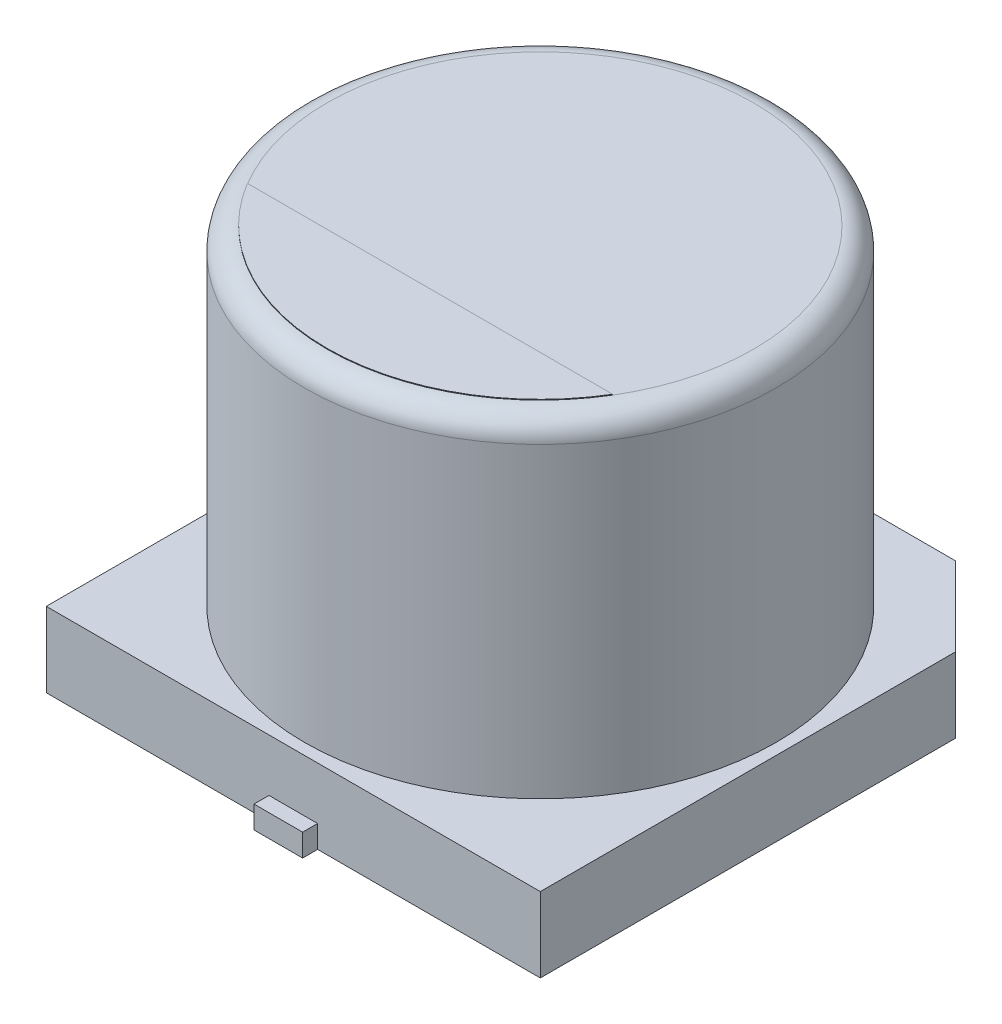
SolidWorks part; units mm, degrees
ref_plane "Front Plane" through (0, 0, 0) normal (0, 0, 1) x (1, 0, 0)
ref_plane "Top Plane" through (0, 0, 0) normal (0, 1, 0) x (1, 0, 0)
ref_plane "Right Plane" through (0, 0, 0) normal (1, 0, 0) x (0, 0, -1)
sketch "Sketch2" plane through (0, 0, 0) normal (0, 1, 0) x (1, 0, 0)
  line L0 (0, 0) -> (0, 2.085) construction
  line L1 (0, 0) -> (2.9643, 0) construction
  line L2 (3.3, -3.3) -> (-3.3, -3.3)
  line L3 (-3.3, -3.3) -> (-3.3, 2.25)
  line L4 (-3.3, 2.25) -> (-2.25, 3.3)
  line L5 (-2.25, 3.3) -> (2.25, 3.3)
  line L6 (2.25, 3.3) -> (3.3, 2.25)
  line L7 (3.3, 2.25) -> (3.3, -3.3)
  line L8 (0, -3.3) -> (0, -0.9795) construction
  line L9 (0, 3.3) -> (0, 2.1922) construction
  line L10 (-0.2934, -3.3) -> (-0.2934, 3.3) construction
  line L11 (-0.2934, 0) -> (-0.8682, 0) construction
  dimension "D1" = 6.6
  dimension "D2" = 6.6
  dimension "D3" = 4.5
extrude "Boss-Extrude1" add sketch "Sketch2" along normal blind 1
sketch "Sketch3" plane through (0, 0, 0) normal (0, 1, 0) x (1, 0, 0)
  circle A0 centre (0, 0) radius 3.15
  dimension "D1" = 6.3
extrude "Boss-Extrude2" add sketch "Sketch3" along normal blind 5.4 contours A0
fillet "Fillet1" radius 0.3 1 edges at (0, 5.4, 3.15)
sketch "Sketch4" plane through (0, 0, 0) normal (0, 1, 0) x (1, 0, 0)
  line L0 (0, 0) -> (3.5846, 0) construction
  line L1 (0.325, 3.5) -> (-0.325, 3.5)
  line L2 (0.325, -0.9) -> (-0.325, -0.9)
  line L3 (0.325, -0.9) -> (0.325, -3.5)
  line L4 (0.325, -3.5) -> (-0.325, -3.5)
  line L5 (-0.325, -0.9) -> (-0.325, -3.5)
  line L6 (0.325, -0.9) -> (-0.325, -3.5) construction
  line L7 (0.325, -3.5) -> (-0.325, -0.9) construction
  line L8 (-0.325, 0.9) -> (-0.325, 3.5)
  line L9 (0.325, 0.9) -> (-0.325, 0.9)
  line L10 (0.325, 0.9) -> (0.325, 3.5)
  line L11 (0.325, 3.5) -> (-0.325, 0.9) construction
  line L12 (0.325, 0.9) -> (-0.325, 3.5) construction
  point P1 (0, -2.2)
  point P12 (0, 2.2)
  dimension "D1" = 0.65
  dimension "D2" = 2.6
  dimension "D3" = 1.8
extrude "Boss-Extrude3" add sketch "Sketch4" along normal blind 0.3
ref_plane "Plane1" through (0, 5.4, 0) normal (0, 1, 0) x (1, 0, 0)
sketch "Sketch5" plane through (0, 5.4, 0) normal (0, 1, 0) x (1, 0, 0)
  line L0 (-2.4399, -1.4729) -> (2.4399, -1.4729)
  circle A0 centre (0, 0) radius 2.85 construction
  arc A1 (-2.4399, -1.4729) -> (2.4399, -1.4729) centre (0, 0) ccw
extrude "Boss-Extrude4" add sketch "Sketch5" along normal blind 0.01
